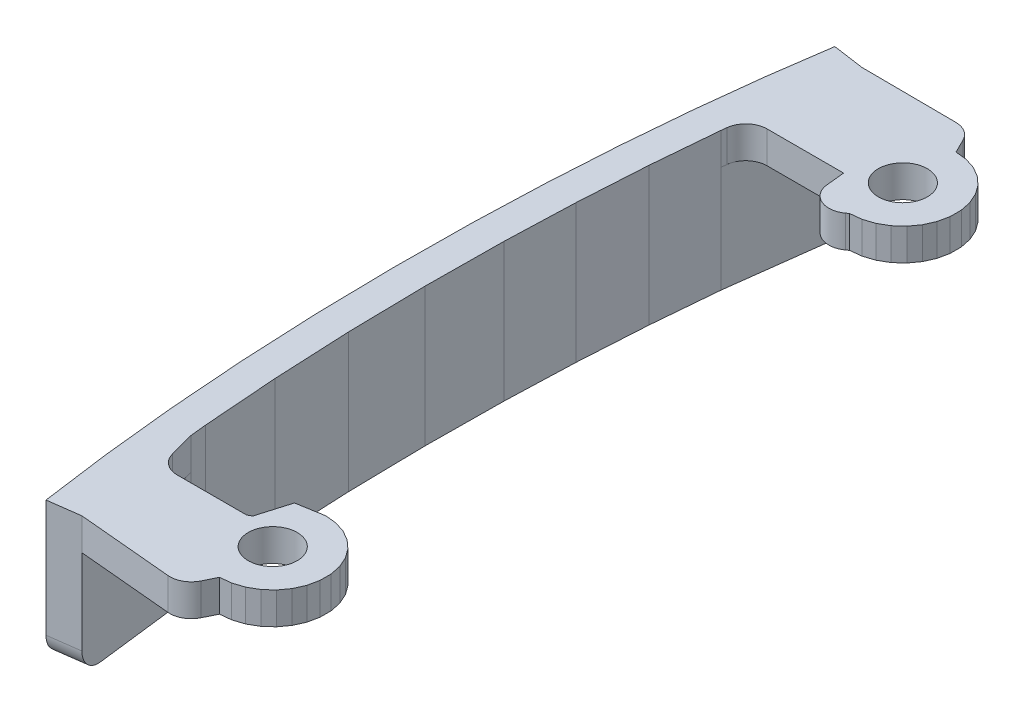
SolidWorks part; units mm, degrees
ref_plane "Płaszczyzna przednia" through (0, 0, 0) normal (0, 0, 1) x (1, 0, 0)
ref_plane "Płaszczyzna górna" through (0, 0, 0) normal (0, 1, 0) x (1, 0, 0)
ref_plane "Płaszczyzna prawa" through (0, 0, 0) normal (1, 0, 0) x (0, 0, -1)
sketch "Szkic2" plane through (0, 0.9904, 0) normal (0, 1, 0) x (1, 0, 0)
  line L0 (-173.5371, -25.6295) -> (-177.9802, -25.6005)
  line L3 (-173.6037, -62.5712) -> (-178.0582, -62.1645)
  line L4 (-179.4653, -25.3891) -> (-179.8753, -28.2702)
  line L5 (-179.8753, -28.2702) -> (-180.2209, -31.3158)
  line L6 (-180.2209, -31.3158) -> (-180.4963, -34.48)
  line L7 (-180.4963, -34.48) -> (-180.6936, -37.7356)
  line L8 (-180.6936, -37.7356) -> (-180.811, -41.0532)
  line L9 (-180.811, -41.0532) -> (-180.8444, -44.7704)
  line L10 (-180.8444, -44.7704) -> (-180.7766, -48.48)
  line L11 (-180.7766, -48.48) -> (-180.6066, -52.1372)
  line L12 (-180.6066, -52.1372) -> (-180.3404, -55.6994)
  line L13 (-180.3404, -55.6994) -> (-179.9818, -59.1279)
  line L14 (-179.9818, -59.1279) -> (-179.5448, -62.3651)
  line L15 (-177.9802, -25.6005) -> (-179.4653, -25.3891)
  line L16 (-178.0582, -62.1645) -> (-179.5448, -62.3651)
  line L17 (-178.8462, -55.5655) -> (-178.4922, -58.9495) construction
  line L18 (-178.7282, -31.4655) -> (-178.7001, -31.2172)
  line L20 (-177.7064, -30.33) -> (-174.1125, -30.33)
  line L22 (-172.3262, -56.4335) -> (-173.5902, -56.6495)
  line L23 (-173.5902, -56.6495) -> (-174.0356, -58.1605)
  line L24 (-174.0356, -58.1605) -> (-174.224, -58.263)
  line L25 (-174.224, -58.263) -> (-177.4828, -58.263)
  line L26 (-178.4487, -57.5219) -> (-178.7651, -56.3415)
  line L28 (-172.4416, -31.9169) -> (-172.3262, -31.8335)
  line L29 (-174.0227, -31.2086) -> (-174.1125, -30.33)
  line L338 (-172.6168, -62.0195) -> (-172.3262, -61.4335)
  line L339 (-172.3262, -61.4335) -> (-171.8062, -61.3785)
  line L340 (-171.8062, -61.3785) -> (-171.3092, -61.2175)
  line L341 (-171.3092, -61.2175) -> (-170.8562, -60.9565)
  line L342 (-170.8562, -60.9565) -> (-170.4682, -60.6065)
  line L343 (-170.4682, -60.6065) -> (-170.1612, -60.1835)
  line L344 (-170.1612, -60.1835) -> (-169.9482, -59.7065)
  line L345 (-169.9482, -59.7065) -> (-169.8402, -59.1945)
  line L346 (-169.8402, -59.1945) -> (-169.8402, -58.6725)
  line L347 (-169.8402, -58.6725) -> (-169.9482, -58.1605)
  line L348 (-169.9482, -58.1605) -> (-170.1612, -57.6835)
  line L349 (-170.1612, -57.6835) -> (-170.4682, -57.2605)
  line L350 (-170.4682, -57.2605) -> (-170.8562, -56.9105)
  line L351 (-170.8562, -56.9105) -> (-171.3092, -56.6495)
  line L352 (-171.3092, -56.6495) -> (-171.8062, -56.4885)
  line L353 (-171.8062, -56.4885) -> (-172.3262, -56.4335)
  line L375 (-172.3262, -31.8335) -> (-171.8062, -31.7785)
  line L376 (-171.8062, -31.7785) -> (-171.3092, -31.6175)
  line L377 (-171.3092, -31.6175) -> (-170.8562, -31.3565)
  line L378 (-170.8562, -31.3565) -> (-170.4682, -31.0065)
  line L379 (-170.4682, -31.0065) -> (-170.1612, -30.5835)
  line L380 (-170.1612, -30.5835) -> (-169.9482, -30.1065)
  line L381 (-169.9482, -30.1065) -> (-169.8402, -29.5945)
  line L382 (-169.8402, -29.5945) -> (-169.8402, -29.0725)
  line L383 (-169.8402, -29.0725) -> (-169.9482, -28.5605)
  line L384 (-169.9482, -28.5605) -> (-170.1612, -28.0835)
  line L385 (-170.1612, -28.0835) -> (-170.4682, -27.6605)
  line L386 (-170.4682, -27.6605) -> (-170.8562, -27.3105)
  line L387 (-170.8562, -27.3105) -> (-171.3092, -27.0495)
  line L388 (-171.3092, -27.0495) -> (-171.8062, -26.8885)
  line L389 (-171.8062, -26.8885) -> (-172.3262, -26.8335)
  line L390 (-172.3262, -26.8335) -> (-172.6477, -26.1852)
  line L438 (-178.7282, -31.4655) -> (-179.0002, -34.5905)
  line L439 (-179.0002, -34.5905) -> (-179.1952, -37.8075)
  line L440 (-179.1952, -37.8075) -> (-179.3112, -41.0865)
  line L441 (-179.3112, -41.0865) -> (-179.3442, -44.7635)
  line L442 (-179.3442, -44.7635) -> (-179.2772, -48.4315)
  line L443 (-179.2772, -48.4315) -> (-179.1092, -52.0465)
  line L444 (-179.1092, -52.0465) -> (-178.8462, -55.5655)
  line L445 (-178.8462, -55.5655) -> (-178.7651, -56.3415)
  line L459 (-178.3872, -28.4605) -> (-178.7282, -31.4655) construction
  line L460 (-177.9802, -25.6005) -> (-178.3872, -28.4605) construction
  line L461 (-178.4922, -58.9495) -> (-178.0582, -62.1645) construction
  arc A0 (-173.5371, -25.6295) -> (-172.6477, -26.1852) centre (-173.5436, -26.6294) cw
  circle A2 centre (-172.326, -29.3335) radius 1.15
  circle A4 centre (-172.326, -58.9335) radius 1.15
  arc A5 (-178.7001, -31.2172) -> (-177.7064, -30.33) centre (-177.7064, -31.33) cw
  arc A6 (-178.4487, -57.5219) -> (-177.4828, -58.263) centre (-177.4828, -57.263) ccw
  arc A7 (-172.6168, -62.0195) -> (-173.6037, -62.5712) centre (-173.5127, -61.5753) cw
  arc A8 (-172.4416, -31.9169) -> (-174.0227, -31.2086) centre (-173.0278, -31.1068) cw
  point P60 (-178.5994, -30.33)
  dimension "D5" = 1
  dimension "D6" = 1
  dimension "D4" = 1.5
extrude "Dodanie-wyciągnięcie1" add sketch "Szkic2" along normal blind 1.5
sketch "Szkic3" plane through (0, 0.9904, 0) normal (0, -1, 0) x (1, 0, 0)
  line L0 (-178.7651, 56.3415) -> (-178.0582, 62.1645)
  line L1 (-178.0582, 62.1645) -> (-179.5448, 62.3651)
  line L2 (-179.4653, 25.3891) -> (-177.9802, 25.6005)
  line L3 (-177.9802, 25.6005) -> (-178.7282, 31.4655)
  line L64 (-179.4653, 25.3891) -> (-177.9802, 25.6005)
  line L65 (-177.9802, 25.6005) -> (-173.5371, 25.6295)
  line L66 (-172.6477, 26.1852) -> (-172.3262, 26.8335)
  line L67 (-172.3262, 26.8335) -> (-171.8062, 26.8885)
  line L68 (-171.8062, 26.8885) -> (-171.3092, 27.0495)
  line L69 (-171.3092, 27.0495) -> (-170.8562, 27.3105)
  line L70 (-170.8562, 27.3105) -> (-170.4682, 27.6605)
  line L71 (-170.4682, 27.6605) -> (-170.1612, 28.0835)
  line L72 (-170.1612, 28.0835) -> (-169.9482, 28.5605)
  line L73 (-169.9482, 28.5605) -> (-169.8402, 29.0725)
  line L74 (-169.8402, 29.0725) -> (-169.8402, 29.5945)
  line L75 (-169.8402, 29.5945) -> (-169.9482, 30.1065)
  line L76 (-169.9482, 30.1065) -> (-170.1612, 30.5835)
  line L77 (-170.1612, 30.5835) -> (-170.4682, 31.0065)
  line L78 (-170.4682, 31.0065) -> (-170.8562, 31.3565)
  line L79 (-170.8562, 31.3565) -> (-171.3092, 31.6175)
  line L80 (-171.3092, 31.6175) -> (-171.8062, 31.7785)
  line L81 (-171.8062, 31.7785) -> (-172.3262, 31.8335)
  line L82 (-172.3262, 31.8335) -> (-172.4416, 31.9169)
  line L83 (-174.0227, 31.2086) -> (-174.1125, 30.33)
  line L84 (-174.1125, 30.33) -> (-177.7064, 30.33)
  line L85 (-178.7001, 31.2172) -> (-178.7282, 31.4655)
  line L86 (-178.7282, 31.4655) -> (-179.0002, 34.5905)
  line L87 (-179.0002, 34.5905) -> (-179.1952, 37.8075)
  line L88 (-179.1952, 37.8075) -> (-179.3112, 41.0865)
  line L89 (-179.3112, 41.0865) -> (-179.3442, 44.7635)
  line L90 (-179.3442, 44.7635) -> (-179.2772, 48.4315)
  line L91 (-179.2772, 48.4315) -> (-179.1092, 52.0465)
  line L92 (-179.1092, 52.0465) -> (-178.8462, 55.5655)
  line L93 (-178.8462, 55.5655) -> (-178.7651, 56.3415)
  line L94 (-178.7651, 56.3415) -> (-178.4487, 57.5219)
  line L95 (-177.4828, 58.263) -> (-174.224, 58.263)
  line L96 (-174.224, 58.263) -> (-174.0356, 58.1605)
  line L97 (-174.0356, 58.1605) -> (-173.5902, 56.6495)
  line L98 (-173.5902, 56.6495) -> (-172.3262, 56.4335)
  line L99 (-172.3262, 56.4335) -> (-171.8062, 56.4885)
  line L100 (-171.8062, 56.4885) -> (-171.3092, 56.6495)
  line L101 (-171.3092, 56.6495) -> (-170.8562, 56.9105)
  line L102 (-170.8562, 56.9105) -> (-170.4682, 57.2605)
  line L103 (-170.4682, 57.2605) -> (-170.1612, 57.6835)
  line L104 (-170.1612, 57.6835) -> (-169.9482, 58.1605)
  line L105 (-169.9482, 58.1605) -> (-169.8402, 58.6725)
  line L106 (-169.8402, 58.6725) -> (-169.8402, 59.1945)
  line L107 (-169.8402, 59.1945) -> (-169.9482, 59.7065)
  line L108 (-169.9482, 59.7065) -> (-170.1612, 60.1835)
  line L109 (-170.1612, 60.1835) -> (-170.4682, 60.6065)
  line L110 (-170.4682, 60.6065) -> (-170.8562, 60.9565)
  line L111 (-170.8562, 60.9565) -> (-171.3092, 61.2175)
  line L112 (-171.3092, 61.2175) -> (-171.8062, 61.3785)
  line L113 (-171.8062, 61.3785) -> (-172.3262, 61.4335)
  line L114 (-172.3262, 61.4335) -> (-172.6168, 62.0195)
  line L115 (-173.6037, 62.5712) -> (-178.0582, 62.1645)
  line L116 (-178.0582, 62.1645) -> (-179.5448, 62.3651)
  line L117 (-179.5448, 62.3651) -> (-179.9818, 59.1279)
  line L118 (-179.9818, 59.1279) -> (-180.3404, 55.6994)
  line L119 (-180.3404, 55.6994) -> (-180.6066, 52.1372)
  line L120 (-180.6066, 52.1372) -> (-180.7766, 48.48)
  line L121 (-180.7766, 48.48) -> (-180.8444, 44.7704)
  line L122 (-180.8444, 44.7704) -> (-180.811, 41.0532)
  line L123 (-180.811, 41.0532) -> (-180.6936, 37.7356)
  line L124 (-180.6936, 37.7356) -> (-180.4963, 34.48)
  line L125 (-180.4963, 34.48) -> (-180.2209, 31.3158)
  line L126 (-180.2209, 31.3158) -> (-179.8753, 28.2702)
  line L127 (-179.8753, 28.2702) -> (-179.4653, 25.3891)
  line L150 (-178.7282, 31.4655) -> (-179.0002, 34.5905)
  line L151 (-179.0002, 34.5905) -> (-179.1952, 37.8075)
  line L152 (-179.1952, 37.8075) -> (-179.3112, 41.0865)
  line L153 (-179.3112, 41.0865) -> (-179.3442, 44.7635)
  line L154 (-179.3442, 44.7635) -> (-179.2772, 48.4315)
  line L155 (-179.2772, 48.4315) -> (-179.1092, 52.0465)
  line L156 (-179.1092, 52.0465) -> (-178.8462, 55.5655)
  line L157 (-178.8462, 55.5655) -> (-178.7651, 56.3415)
  line L181 (-179.5448, 62.3651) -> (-179.9818, 59.1279)
  line L182 (-179.9818, 59.1279) -> (-180.3404, 55.6994)
  line L183 (-180.3404, 55.6994) -> (-180.6066, 52.1372)
  line L184 (-180.6066, 52.1372) -> (-180.7766, 48.48)
  line L185 (-180.7766, 48.48) -> (-180.8444, 44.7704)
  line L186 (-180.8444, 44.7704) -> (-180.811, 41.0532)
  line L187 (-180.811, 41.0532) -> (-180.6936, 37.7356)
  line L188 (-180.6936, 37.7356) -> (-180.4963, 34.48)
  line L189 (-180.4963, 34.48) -> (-180.2209, 31.3158)
  line L190 (-180.2209, 31.3158) -> (-179.8753, 28.2702)
  line L191 (-179.8753, 28.2702) -> (-179.4653, 25.3891)
  arc A5 (-173.5371, 25.6295) -> (-172.6477, 26.1852) centre (-173.5436, 26.6294) ccw
  arc A6 (-172.4416, 31.9169) -> (-174.0227, 31.2086) centre (-173.0278, 31.1068) ccw
  arc A7 (-178.7001, 31.2172) -> (-177.7064, 30.33) centre (-177.7064, 31.33) ccw
  arc A8 (-177.4828, 58.263) -> (-178.4487, 57.5219) centre (-177.4828, 57.263) ccw
  arc A9 (-172.6168, 62.0195) -> (-173.6037, 62.5712) centre (-173.5127, 61.5753) ccw
  dimension "D1" = 0
extrude "Dodanie-wyciągnięcie2" add sketch "Szkic3" along normal blind 5
fillet "Zaokrąglenie1" radius 1 2 edges at (-178.8015, -4.0096, 62.2648) (-178.7228, -4.0096, 25.4948)
